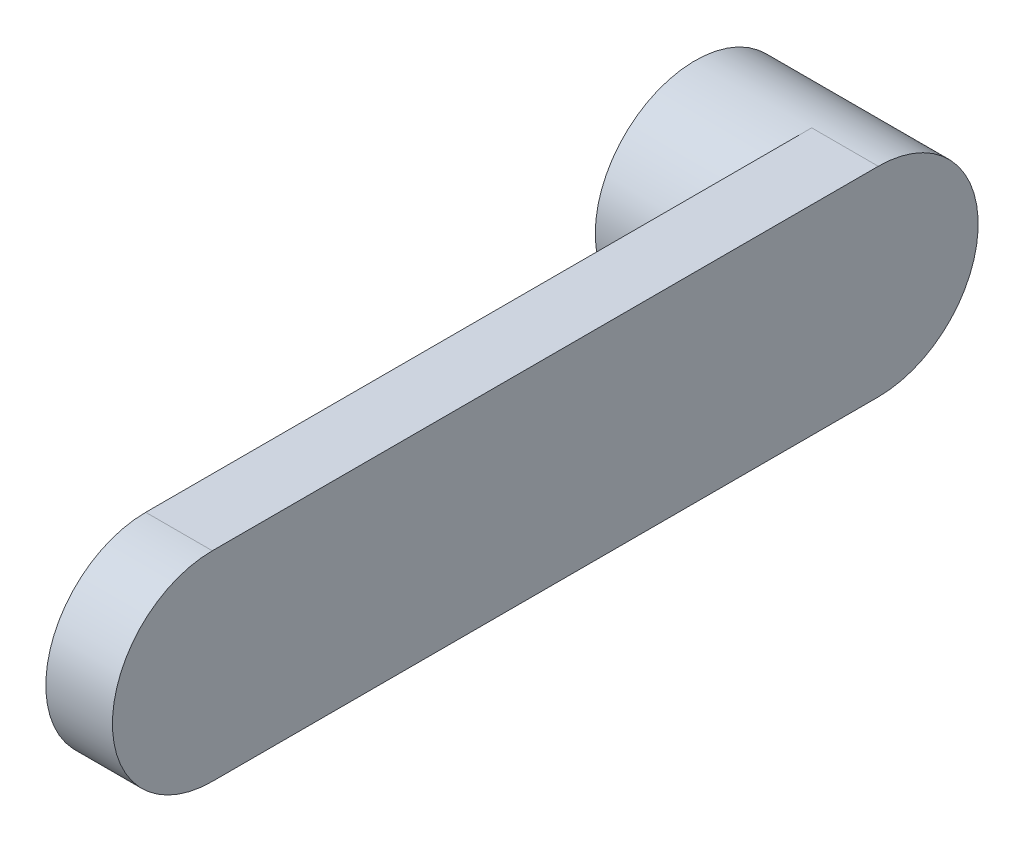
SolidWorks part; units mm, degrees
ref_plane "前视基准面" through (0, 0, 0) normal (0, 0, 1) x (1, 0, 0)
ref_plane "上视基准面" through (0, 0, 0) normal (0, 1, 0) x (1, 0, 0)
ref_plane "右视基准面" through (0, 0, 0) normal (1, 0, 0) x (0, 0, -1)
sketch "草图1" plane through (0, 0, 0) normal (1, 0, 0) x (0, 0, -1)
  line L0 (0, 30) -> (-200, 30)
  line L1 (0, -30) -> (-200, -30)
  arc A1 (0, 30) -> (0, -30) centre (0, 0) cw
  arc A2 (-200, 30) -> (-200, -30) centre (-200, 0) ccw
extrude "凸台-拉伸1" add sketch "草图1" along normal blind 20
sketch "草图2" plane through (0, 0, 0) normal (-1, 0, 0) x (0, 0, 1)
  circle A0 centre (0, 0) radius 30
extrude "凸台-拉伸2" add sketch "草图2" along normal blind 35
